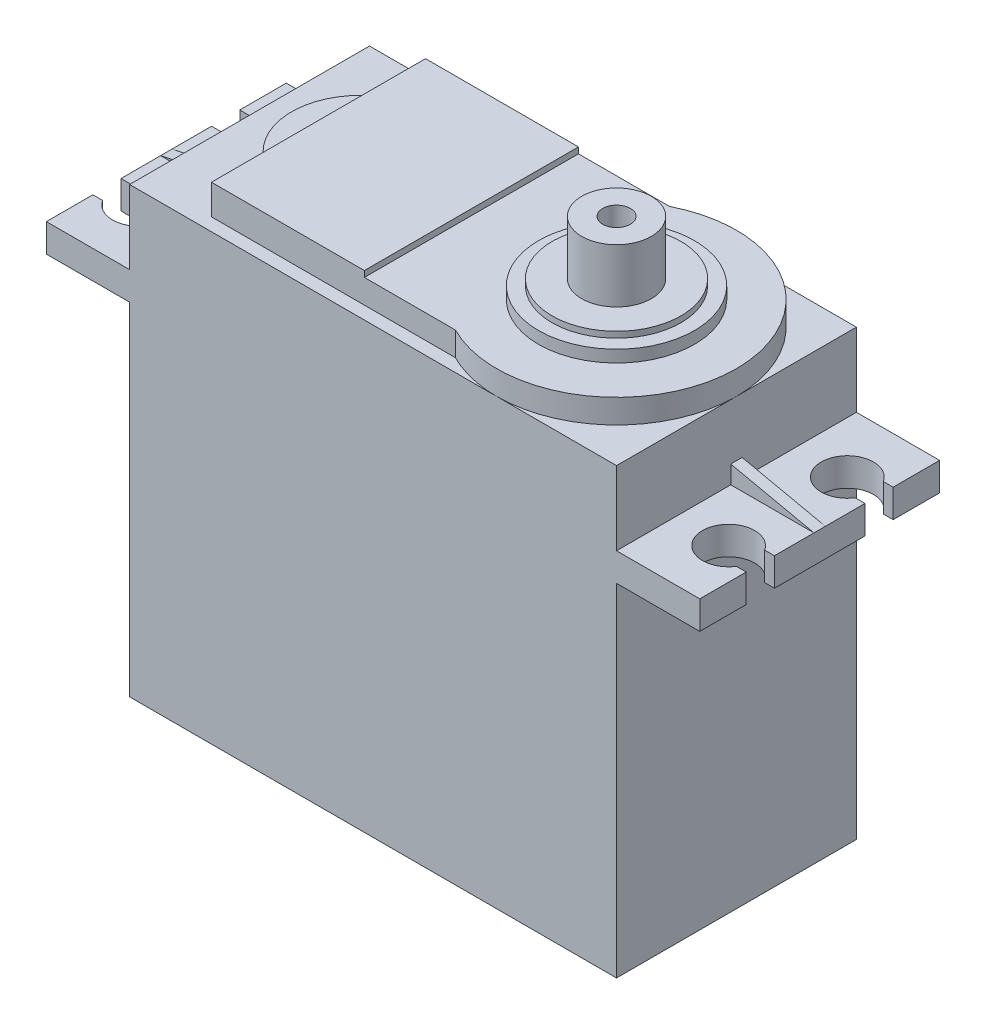
SolidWorks part; units mm, degrees
ref_plane "Front Plane" through (0, 0, 0) normal (0, 0, 1) x (1, 0, 0)
ref_plane "Top Plane" through (0, 0, 0) normal (0, 1, 0) x (1, 0, 0)
ref_plane "Right Plane" through (0, 0, 0) normal (1, 0, 0) x (0, 0, -1)
sketch "Sketch1" plane through (0, 0, 0) normal (0, 1, 0) x (1, 0, 0)
  line L1 (-20.3, -10) -> (20.3, -10)
  line L2 (-20.3, -10) -> (-20.3, 10)
  line L3 (-20.3, 10) -> (20.3, 10)
  line L4 (20.3, -10) -> (20.3, 10)
  line L5 (0, 10) -> (0, -10) construction
  line L6 (-20.3, 0) -> (20.3, 0) construction
  point P0 (0, 0)
  dimension "D1" = 40.6
  dimension "D2" = 20
extrude "Boss-Extrude1" add sketch "Sketch1" along normal blind 37
sketch "Sketch2" plane through (0, 0, 0) normal (0, 1, 0) x (1, 0, 0)
  line L0 (-20.3, -10) -> (20.3, -10) construction
  line L1 (20.3, 10) -> (27.24, 10)
  line L2 (20.3, 10) -> (20.3, -10)
  line L3 (20.3, -10) -> (27.24, -10)
  line L4 (27.24, 10) -> (27.24, -10)
  line L5 (23.77, -10) -> (23.77, 10) construction
  line L6 (20.3, 0) -> (27.24, 0) construction
  line L7 (0, 10) -> (0, -10) construction
  line L8 (20.3, 10) -> (-20.3, 10) construction
  point P52 (23.77, 0)
  dimension "D1" = 6.94
extrude "Boss-Extrude2" add sketch "Sketch2" along normal blind 2.35 from offset 28.5
sketch "Sketch10" plane through (0, 0, 0) normal (0, 0, 1) x (1, 0, 0)
  line L4 (20.3, 32.35) -> (27.24, 30.85)
  line L5 (20.3, 37) -> (20.3, 30.85) construction
  line L6 (27.24, 30.85) -> (27.24, 30.3315)
  line L7 (27.24, 30.85) -> (27.24, 28.5) construction
  line L8 (27.24, 30.3315) -> (19.8801, 30.3315)
  line L9 (19.8801, 30.3315) -> (19.8801, 32.35)
  line L10 (19.8801, 32.35) -> (20.3, 32.35)
  line L11 (20.3, 30.85) -> (27.24, 30.85) construction
  point P15 (27.24, 30.3315)
  dimension "D1" = 1.5
extrude "Boss-Extrude8" add sketch "Sketch10" along normal mid plane 0.95 separate body
sketch "Sketch3" plane through (0, 30.85, 0) normal (0, 1, 0) x (1, 0, 0)
  line L0 (24.595, 4.95) -> (24.595, -4.95) construction
  line L3 (27.24, 0) -> (20.3, 0) construction
  line L4 (27.24, -10) -> (27.24, 10) construction
  line L5 (20.3, -10) -> (20.3, 10) construction
  line L6 (0, 10) -> (0, -10) construction
  line L7 (20.3, 10) -> (-20.3, 10) construction
  line L8 (-20.3, -10) -> (20.3, -10) construction
  line L9 (24.595, 4.95) -> (27.24, 4.95) construction
  line L10 (29.885, -6.125) -> (24.595, -6.125)
  line L11 (29.885, 3.775) -> (24.595, 3.775)
  line L12 (29.885, 3.775) -> (29.885, 6.125)
  line L13 (29.885, 6.125) -> (24.595, 6.125)
  line L14 (24.595, 3.775) -> (24.595, 6.125)
  line L15 (27.24, 6.125) -> (27.24, 3.775) construction
  line L16 (29.885, 4.95) -> (24.595, 4.95) construction
  line L17 (24.595, -3.775) -> (24.595, -6.125)
  line L18 (29.885, -3.775) -> (24.595, -3.775)
  line L19 (29.885, -3.775) -> (29.885, -6.125)
  circle A0 centre (24.595, 4.95) radius 2.175
  circle A1 centre (24.595, -4.95) radius 2.175
  point P3 (24.595, 0)
  line M5 (27.24, -10) -> (27.24, 10)
  dimension "D3" = 4.35
  dimension "D1" = 9.9
  dimension "D2" = 2.645
  dimension "D4" = 2.35
extrude "Cut-Extrude2" cut sketch "Sketch3" against normal through all contours L13 A0 L11 L14 | L12 L13 L11 M5 | L11 A0 L13 L14 | A0 L11 L13 M5 | L18 A1 L10 L17 | L10 A1 L18 L17 | L19 L18 L10 M5 | A1 L10 L18 M5
mirror "Mirror2" about plane through (0, 0, 0) normal (1, 0, 0) of "Cut-Extrude2", "Boss-Extrude2"
mirror "Mirror6" about plane through (0, 0, 0) normal (1, 0, 0) of "Boss-Extrude8"
sketch "Sketch5" plane through (0, 37, 0) normal (0, 1, 0) x (1, 0, 0)
  line L0 (-20.3, 0) -> (20.3, 0) construction
  line L1 (-20.3, 10) -> (-20.3, -10) construction
  line L2 (20.3, 10) -> (20.3, -10) construction
  line L3 (-20.3, 10) -> (-20.3, 0.475) construction
  line L4 (-14.55, -8.925) -> (10.45, -8.925)
  line L5 (-14.55, -8.925) -> (-14.55, 8.925)
  line L6 (-14.55, 8.925) -> (10.45, 8.925)
  line L7 (10.45, -8.925) -> (10.45, 8.925)
  line L8 (-2.05, 8.925) -> (-2.05, -8.925) construction
  line L9 (-14.55, 0) -> (10.45, 0) construction
  circle A0 centre (10.3, 0) radius 10
  circle A1 centre (-11.0744, 0) radius 5.7256
  point P6 (-2.05, 0)
  point P16 (-14.55, 4.55)
  point P17 (-14.55, -4.55)
  point P18 (-16.8, 0)
  dimension "D4" = 20
  dimension "D5" = 9.1
  dimension "D1" = 17.85
  dimension "D2" = 25
  dimension "D3" = 5.75
  dimension "D6" = 3.5
extrude "Boss-Extrude4" add sketch "Sketch5" along normal blind 2 contours A0 L6 L5 L4 | L6 A0 L4 L7 | A0 L6 L7 L4 | A1
sketch "Sketch6" plane through (0, 39, 0) normal (0, 1, 0) x (1, 0, 0)
  line L0 (-20.3, 0) -> (20.3, 0) construction
  line L1 (-20.3, 10) -> (-20.3, -10) construction
  line L2 (-14.55, -8.925) -> (5.7895, -8.925) construction
  line L3 (-14.55, 8.925) -> (-1.8, 8.925)
  line L4 (-14.55, 8.925) -> (-14.55, -8.925)
  line L5 (-14.55, -8.925) -> (-1.8, -8.925)
  line L6 (-1.8, 8.925) -> (-1.8, -8.925)
  line L7 (-8.175, -8.925) -> (-8.175, 8.925) construction
  line L8 (-14.55, 0) -> (-1.8, 0) construction
  point P65 (-8.175, 0)
  dimension "D1" = 12.75
extrude "Boss-Extrude5" add sketch "Sketch6" along normal blind 0.5
sketch "Sketch7" plane through (0, 39, 0) normal (0, 1, 0) x (1, 0, 0)
  circle A0 centre (10.3, 0) radius 6.5
  dimension "D1" = 13
extrude "Boss-Extrude6" add sketch "Sketch7" along normal blind 1
sketch "Sketch8" plane through (0, 40, 0) normal (0, 1, 0) x (1, 0, 0)
  circle A0 centre (10.3, 0) radius 5.375
  dimension "D1" = 10.75
extrude "Boss-Extrude7" add sketch "Sketch8" along normal blind 0.5
sketch "Sketch4" plane through (0, 37, 0) normal (0, 1, 0) x (1, 0, 0)
  circle A0 centre (10.3, 0) radius 2.9
  circle A1 centre (10.3, 0) radius 1.15
  point P0 (10.3, 0)
  dimension "D1" = 5.8
  dimension "D2" = 2.3
extrude "Boss-Extrude3" add sketch "Sketch4" along normal blind 6 from surface at 2 starting at face at (10.3, 39, 6.5)
equation "\"5沒買\"=36.6"
